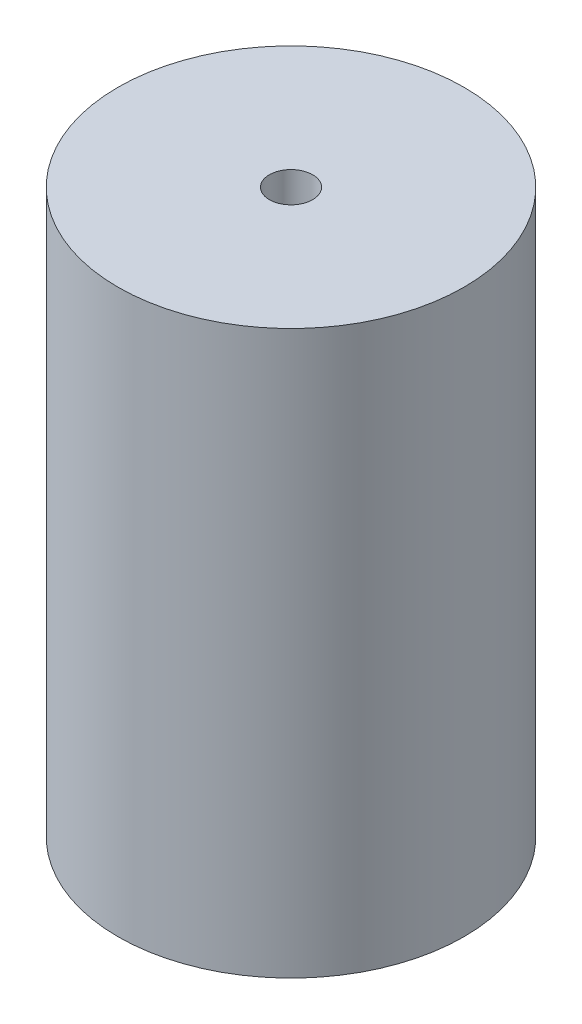
SolidWorks part; units mm, degrees
ref_plane "Front Plane" through (0, 0, 0) normal (0, 0, 1) x (1, 0, 0)
ref_plane "Top Plane" through (0, 0, 0) normal (0, 1, 0) x (1, 0, 0)
ref_plane "Right Plane" through (0, 0, 0) normal (1, 0, 0) x (0, 0, -1)
sketch "Sketch1" plane through (0, 0, 0) normal (0, 1, 0) x (1, 0, 0)
  circle A0 centre (0, 0) radius 50.8
  circle A1 centre (0, 0) radius 6.35
  dimension "D1" = 101.6
  dimension "D2" = 12.7
extrude "Boss-Extrude1" add sketch "Sketch1" along normal blind 165.1
